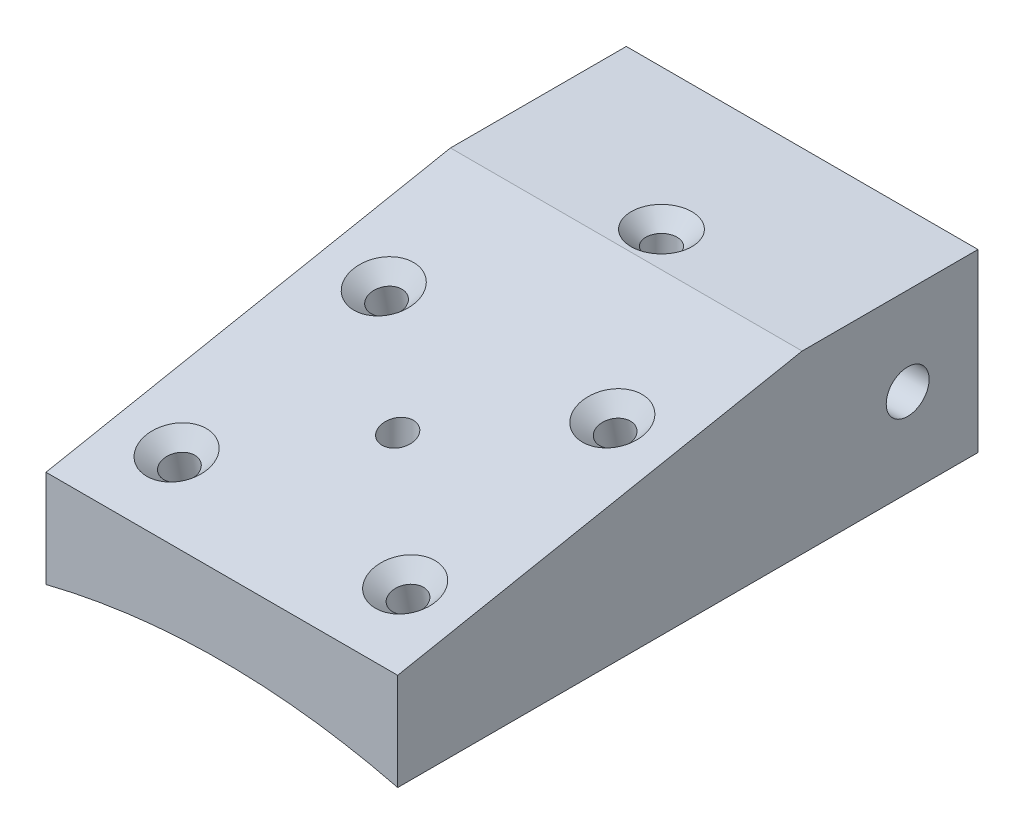
SolidWorks part; units mm, degrees
material "6061-T6 (SS)"
ref_plane "Front Plane" through (0, 0, 0) normal (0, 0, 1) x (1, 0, 0)
ref_plane "Top Plane" through (0, 0, 0) normal (0, 1, 0) x (1, 0, 0)
ref_plane "Right Plane" through (0, 0, 0) normal (1, 0, 0) x (0, 0, -1)
sketch "Sketch1" plane through (0, 0, 0) normal (0, 0, 1) x (1, 0, 0)
  line L0 (0, 0) -> (0, -17.6767) construction
  line L1 (0, 41.016) -> (-33.3169, 41.016) construction
  line L2 (-10, 39.7783) -> (-10, 51.016)
  line L3 (-10, 51.016) -> (10, 51.016)
  line L4 (10, 39.7783) -> (10, 51.016)
  line L5 (-18.4145, 22.6015) -> (10, 51.016) construction
  line L6 (-10, 51.016) -> (16.0762, 24.9398) construction
  arc A0 (10, 39.7783) -> (-10, 39.7783) centre (0, 0) ccw
  point P1 (0, 51.016)
  point P3 (0, 41.016)
  dimension "D1" = 41.016
  dimension "D2" = 20
  dimension "D3" = 10
extrude "Boss-Extrude1" add sketch "Sketch1" along normal mid plane 23
hole_wizard "#2-56 Tapped Hole3" positions "Sketch9" profile "Sketch8" tap size "#2-56" standard "ANSI Inch" end condition through all
sketch "Sketch9" plane through (0, 51.016, 0) normal (0, 1, 0) x (1, 0, 0)
  line L0 (0, 0) -> (0, -2.7876) construction
  line L1 (10, -11.5) -> (-10, -11.5) construction
  point P0 (0, -1.5)
  dimension "D1" = 10
sketch "Sketch8" plane through (0, 51.016, 1.5) normal (1, 0, 0) x (0, 0, 1)
  line L0 (0, 0) -> (0, 11.2377)
  line L1 (0, 11.2377) -> (0.889, 11.2377)
  line L2 (0.889, 11.2377) -> (0.889, 0.8382)
  line L3 (0.889, 0.8382) -> (1.7272, 0)
  line L5 (1.7272, 0) -> (0, 0)
  line L6 (-0.889, 0.8382) -> (-1.7272, 0) construction
  line L11 (0, -6.35) -> (0, 107.95) construction
  dimension "Thru Tap Drill Dia." = 1.778
  dimension "Thru Tap Drill Depth" = 11.2377
  dimension "Near C'Sink Dia." = 3.4544
  dimension "Near C'Sink Angle" = 90
cosmetic thread "Hole Thread5" parameters "D2"=2.1844
sketch "Sketch2" plane through (0, 0, 0) normal (1, 0, 0) x (0, 0, -1)
  line L0 (-11.5, 45.3075) -> (11.5, 49.7783)
  line L1 (-11.5, 39.7783) -> (-11.5, 51.016) construction
  line L2 (11.5, 39.7783) -> (11.5, 51.016) construction
  line L3 (-11.5, 39.7783) -> (11.5, 39.7783) construction
  line L4 (-11.5, 45.3075) -> (-11.5, 51.016)
  line L5 (-11.5, 51.016) -> (11.5, 51.016)
  line L6 (11.5, 51.016) -> (11.5, 49.7783)
  line L7 (-11.5, 51.016) -> (11.5, 51.016) construction
  line L8 (-11.5, 39.7783) -> (11.5, 39.7783) construction
  dimension "D1" = 11
  dimension "D2" = 10
extrude "Cut-Extrude1" cut sketch "Sketch2" against normal mid plane 20
hole_wizard "#2-56 Tapped Hole1" positions "Sketch4" profile "Sketch3" tap size "#2-56" standard "ANSI Inch" end condition through all
sketch "Sketch4" plane through (0, 45.812, 8.9049) normal (0, 0.9816, 0.1908) x (1, 0, 0)
  line L0 (0, 0) -> (0, 5.7186) construction
  line L1 (-10, -2.6436) -> (10, -2.6436) construction
  line L2 (6.5, 1.3564) -> (6.5, 4.3573) construction
  point P0 (6.5, 1.3564)
  point P9 (6.5, 13.3564)
  point P18 (-6.5, 13.3564)
  point P19 (-6.5, 1.3564)
  dimension "D1" = 4
  dimension "D2" = 12
  dimension "D3" = 6.5
cosmetic thread "Hole Thread1" parameters "D2"=2.1844
cosmetic thread "Hole Thread2" parameters "D2"=2.1844
sketch "Sketch3" plane through (6.5, 46.0708, 7.5735) normal (1, 0, 0) x (0, -0.1908, 0.9816)
  line L0 (0, 0) -> (0, 9.8163)
  line L1 (0, 9.8163) -> (0.889, 9.8163)
  line L2 (0.889, 9.8163) -> (0.889, 0.8382)
  line L3 (0.889, 0.8382) -> (1.7272, 0)
  line L5 (1.7272, 0) -> (0, 0)
  line L6 (-0.889, 0.8382) -> (-1.7272, 0) construction
  line L11 (0, -6.35) -> (0, 107.95) construction
  dimension "Thru Tap Drill Dia." = 1.778
  dimension "Thru Tap Drill Depth" = 9.8163
  dimension "Near C'Sink Dia." = 3.4544
  dimension "Near C'Sink Angle" = 90
cosmetic thread "Hole Thread3" parameters "D2"=2.1844
cosmetic thread "Hole Thread4" parameters "D2"=2.1844
sketch "Sketch5" plane through (0, 0, -11.5) normal (0, 0, -1) x (-1, 0, 0)
  line L4 (10, 39.7783) -> (10, 49.7783)
  line L5 (10, 49.7783) -> (-10, 49.7783)
  line L6 (-10, 49.7783) -> (-10, 39.7783)
  line L7 (10, 39.7783) -> (10, 49.7783)
  line L8 (10, 49.7783) -> (-10, 49.7783)
  line L9 (-10, 49.7783) -> (-10, 39.7783)
  arc A1 (10, 39.7783) -> (-10, 39.7783) centre (0, 0) ccw
  arc A2 (10, 39.7783) -> (-10, 39.7783) centre (0, 0) ccw
  dimension "D1" = 0
extrude "Boss-Extrude2" add sketch "Sketch5" along normal blind 10
hole_wizard "#2-56 Tapped Hole4" positions "Sketch11" profile "Sketch10" tap size "#2-56" standard "ANSI Inch" end condition through all
sketch "Sketch11" plane through (0, 49.7783, 0) normal (0, 1, 0) x (1, 0, 0)
  line L0 (0, 0) -> (0, 10.0349) construction
  circle A0 centre (0, -1.5) radius 0.889 construction
  point P0 (0, 13.5)
  dimension "D1" = 15
sketch "Sketch10" plane through (0, 49.7783, -13.5) normal (1, 0, 0) x (0, 0, 1)
  line L0 (0, 0) -> (0, 10)
  line L1 (0, 10) -> (0.889, 10)
  line L2 (0.889, 10) -> (0.889, 0.8382)
  line L3 (0.889, 0.8382) -> (1.7272, 0)
  line L5 (1.7272, 0) -> (0, 0)
  line L6 (-0.889, 0.8382) -> (-1.7272, 0) construction
  line L11 (0, -6.35) -> (0, 107.95) construction
  dimension "Thru Tap Drill Dia." = 1.778
  dimension "Thru Tap Drill Depth" = 10
  dimension "Near C'Sink Dia." = 3.4544
  dimension "Near C'Sink Angle" = 90
cosmetic thread "Hole Thread6" parameters "D2"=2.1844
hole_wizard "#2 Clearance Hole1" positions "Sketch13" profile "Sketch12" hole size "#2" standard "ANSI Inch" end condition through all
sketch "Sketch13" plane through (-10, 0, 0) normal (-1, 0, 0) x (0, 0, 1)
  line L0 (-21.5, 44.7783) -> (-24.3841, 44.7783) construction
  line L1 (-21.5, 39.7783) -> (-21.5, 49.7783) construction
  line L3 (11.5, 45.3075) -> (11.5, 39.7783) construction
  point P8 (-17.5, 44.7783)
  dimension "D1" = 29
sketch "Sketch12" plane through (-10, 44.7783, -17.5) normal (0, 1, 0) x (0, 0, 1)
  line L0 (0, 0) -> (0, 20)
  line L1 (0, 20) -> (1.2192, 20)
  line L2 (1.2192, 20) -> (1.2192, 0)
  line L5 (1.2192, 0) -> (0, 0)
  line L11 (0, -6.35) -> (0, 107.95) construction
  dimension "Thru Hole Dia." = 2.4384
  dimension "Thru Hole Depth" = 20
